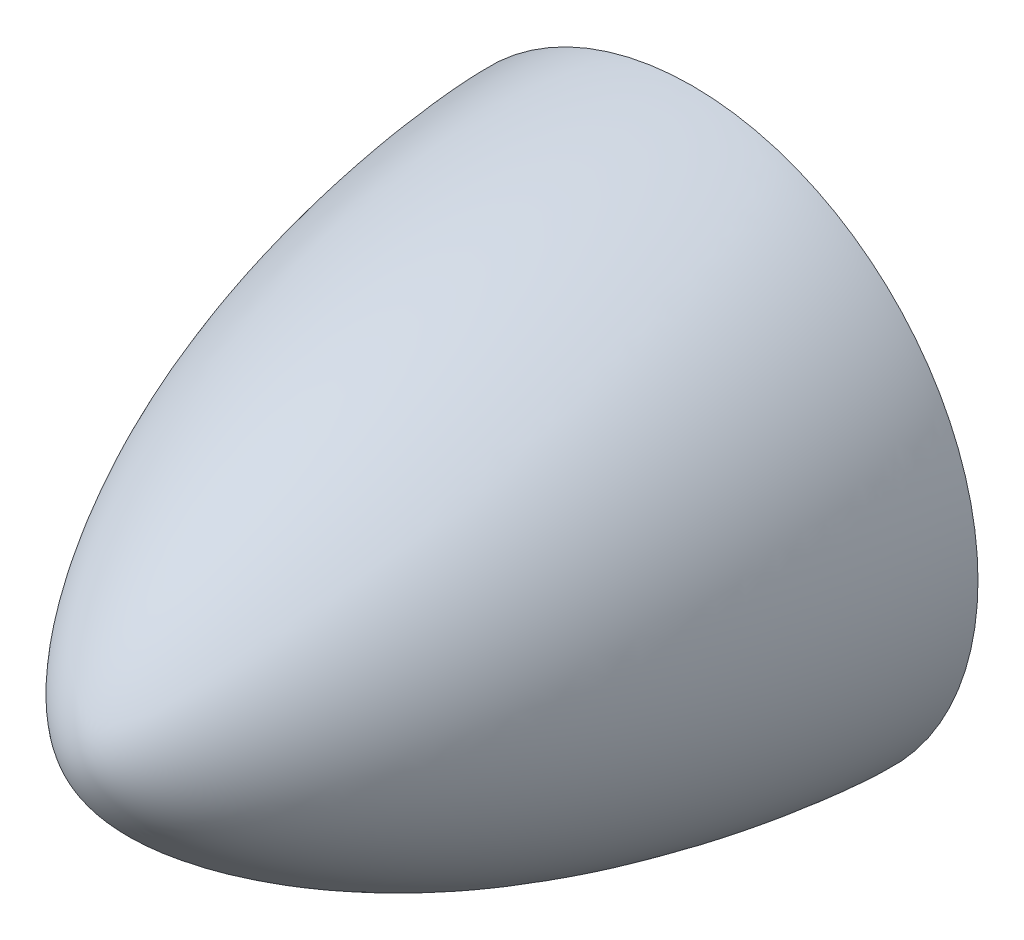
SolidWorks part; units mm, degrees
ref_plane "Front Plane" through (0, 0, 0) normal (0, 0, 1) x (1, 0, 0)
ref_plane "Top Plane" through (0, 0, 0) normal (0, 1, 0) x (1, 0, 0)
ref_plane "Right Plane" through (0, 0, 0) normal (1, 0, 0) x (0, 0, -1)
sketch "Sketch2"
  line L0 (225.1375, -360.4976) -> (1737.8401, -360.4976) construction
  line L1 (0, 0) -> (0, 37.4897)
  line L2 (-80, 0) -> (0, 0)
  spline S0 degree 3 poles (-80, 0) (-80, 8.7954) (-45.5781, 33.8883) (-6.5208, 37.4897) (0, 37.4897) knots 0 0 0 0 0.444533 1 1 1 1
revolve "Revolve1" add sketch "Sketch2" angle 360 about L2
